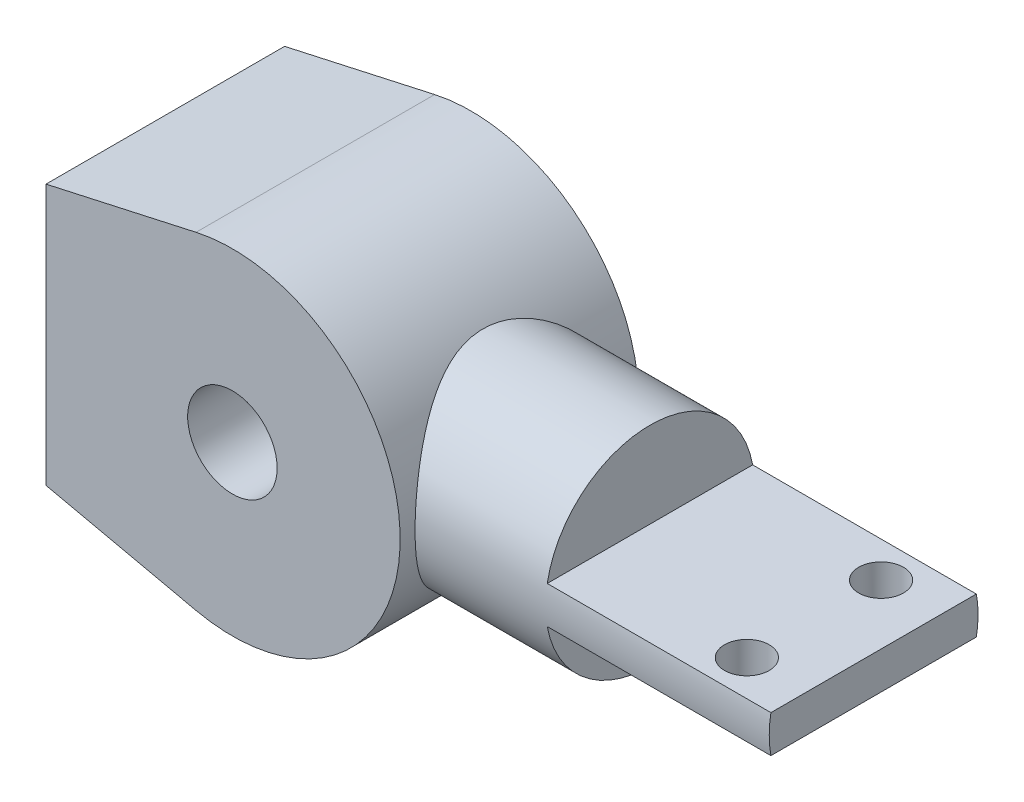
SolidWorks part; units mm, degrees
ref_plane "Ön Düzlem" through (0, 0, 0) normal (0, 0, 1) x (1, 0, 0)
ref_plane "Üst Düzlem" through (0, 0, 0) normal (0, 1, 0) x (1, 0, 0)
ref_plane "Sağ Düzlem" through (0, 0, 0) normal (1, 0, 0) x (0, 0, -1)
sketch "Çizim1" plane through (0, 0, 0) normal (0, 0, 1) x (1, 0, 0)
  line L0 (-25, 17.5) -> (-25, -17.5)
  line L1 (-4.874, 21.9658) -> (-25, 17.5)
  line L2 (-4.874, -21.9658) -> (-25, -17.5)
  arc A0 (-4.874, -21.9658) -> (-4.874, 21.9658) centre (0, 0) ccw
  circle A1 centre (0, 0) radius 6
  point P5 (-25, 0)
  dimension "D1" = 22.5
  dimension "D4" = 12
  dimension "D2" = 25
  dimension "D3" = 35
extrude "Yükseklik-Ekstrüzyon1" add sketch "Çizim1" along normal mid plane 32
ref_plane "Düzlem1" through (40, 0, 0) normal (1, 0, 0) x (0, 0, -1)
sketch "Çizim2" plane through (40, 0, 0) normal (1, 0, 0) x (0, 0, -1)
  circle A0 centre (0, 0) radius 14
  dimension "D1" = 28
extrude "Yükseklik-Ekstrüzyon2" add sketch "Çizim2" against normal up to next
sketch "Çizim3" plane through (40, 0, 0) normal (1, 0, 0) x (0, 0, -1)
  line L1 (-19.6807, -2.5) -> (19.6807, -2.5)
  line L2 (-19.6807, -2.5) -> (-19.6807, 2.5)
  line L3 (-19.6807, 2.5) -> (19.6807, 2.5)
  line L4 (19.6807, -2.5) -> (19.6807, 2.5)
  line L5 (-19.6807, -2.5) -> (19.6807, 2.5) construction
  line L6 (-19.6807, 2.5) -> (19.6807, -2.5) construction
  point P0 (0, 0)
  circle M2 centre (0, 0) radius 14
  dimension "D1" = 5
extrude "Yükseklik-Ekstrüzyon3" add sketch "Çizim3" along normal blind 30 contours L3 L1 M2
sketch "Çizim4" plane through (0, 2.5, 0) normal (0, 1, 0) x (1, 0, 0)
  line L0 (70, -13.775) -> (70, 13.775) construction
  line L2 (0, 0) -> (95.3712, 0) construction
  circle A0 centre (62, -9) radius 3
  circle A1 centre (62, 9) radius 3
  dimension "D1" = 6
  dimension "D2" = 8
  dimension "D3" = 9
extrude "Kes-Ekstrüzyon1" cut sketch "Çizim4" against normal blind 30
